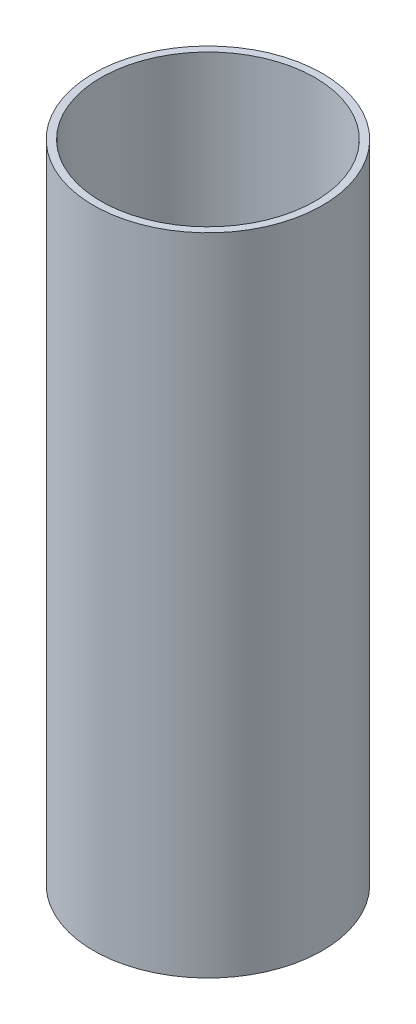
SolidWorks part; units mm, degrees
ref_plane "Front Plane" through (0, 0, 0) normal (0, 0, 1) x (1, 0, 0)
ref_plane "Top Plane" through (0, 0, 0) normal (0, 1, 0) x (1, 0, 0)
ref_plane "Right Plane" through (0, 0, 0) normal (1, 0, 0) x (0, 0, -1)
sketch "Sketch1" plane through (0, 0, 0) normal (0, 0, 1) x (1, 0, 0)
  line L1 (46.355, 0) -> (49.53, 0)
  line L2 (46.355, 0) -> (46.355, 279.4)
  line L3 (46.355, 279.4) -> (49.53, 279.4)
  line L4 (49.53, 0) -> (49.53, 279.4)
  dimension "D1" = 49.53
  dimension "D2" = 3.175
  dimension "D3" = 279.4
  dimension "D4" = 0
ref_axis "Axis1" through (0, -13.97, 0) along (0, 1, 0)
revolve "Revolve1" add sketch "Sketch1" angle 360 about axis through (0, -13.97, 0) along (0, 1, 0)
